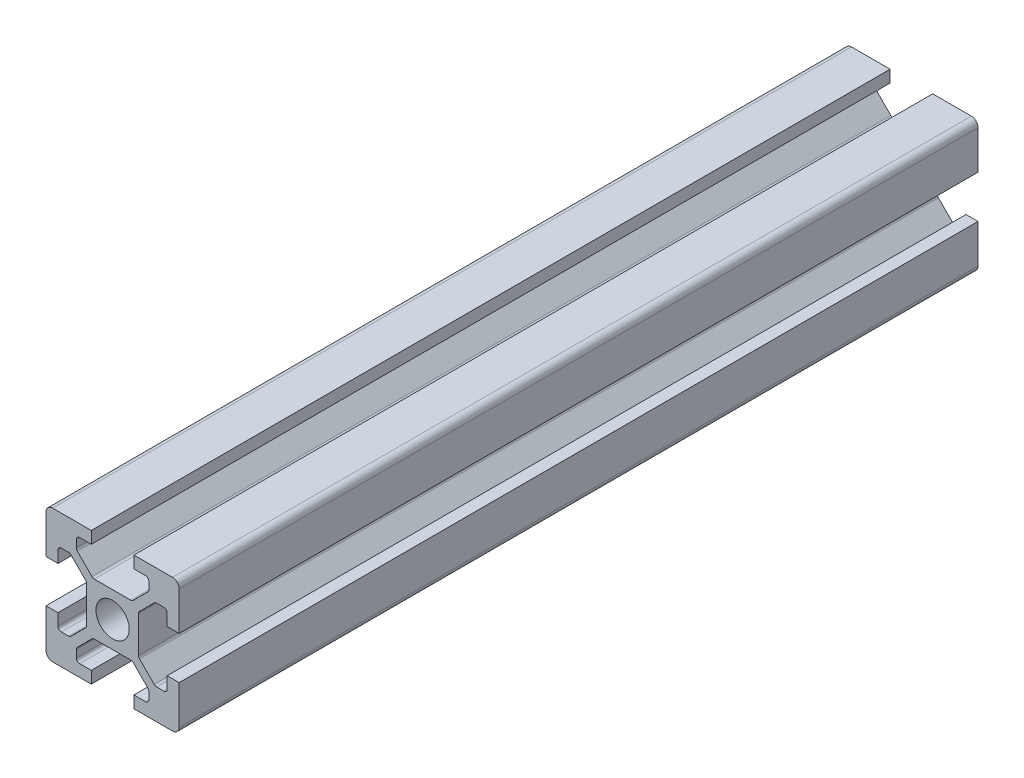
SolidWorks part; units mm, degrees
ref_plane "Front Plane" through (0, 0, 0) normal (0, 0, 1) x (1, 0, 0)
ref_plane "Top Plane" through (0, 0, 0) normal (0, 1, 0) x (1, 0, 0)
ref_plane "Right Plane" through (0, 0, 0) normal (1, 0, 0) x (0, 0, -1)
ref_plane "Plane1" through (0, 0, 0) normal (0, 0, -1) x (-1, 0, 0)
sketch "Sketch1" plane through (0, 0, 0) normal (0, 0, -1) x (-1, 0, 0)
  line L0 (-20, 19) -> (-20, 13.2)
  line L1 (-20, 13.2) -> (-18.2, 13.2)
  line L2 (-18.2, 13.2) -> (-18.2, 14.95)
  line L3 (-17.7, 15.45) -> (-16.6071, 15.45)
  line L4 (-16.2536, 15.3036) -> (-14.0464, 13.0964)
  line L5 (-13.9, 12.7429) -> (-13.9, 7.2571)
  line L6 (-14.0464, 6.9036) -> (-16.2536, 4.6964)
  line L7 (-16.6071, 4.55) -> (-17.7, 4.55)
  line L8 (-18.2, 5.05) -> (-18.2, 6.8)
  line L9 (-18.2, 6.8) -> (-20, 6.8)
  line L10 (-20, 6.8) -> (-20, 1)
  line L11 (-19, 0) -> (-13.2, 0)
  line L12 (-13.2, 0) -> (-13.2, 1.8)
  line L13 (-13.2, 1.8) -> (-14.95, 1.8)
  line L14 (-15.45, 2.3) -> (-15.45, 3.3929)
  line L15 (-15.3036, 3.7464) -> (-13.0964, 5.9536)
  line L16 (-12.7429, 6.1) -> (-7.2571, 6.1)
  line L17 (-6.9036, 5.9536) -> (-4.6964, 3.7464)
  line L18 (-4.55, 3.3929) -> (-4.55, 2.3)
  line L19 (-5.05, 1.8) -> (-6.8, 1.8)
  line L20 (-6.8, 1.8) -> (-6.8, 0)
  line L21 (-6.8, 0) -> (-1, 0)
  line L22 (0, 1) -> (0, 6.8)
  line L23 (0, 6.8) -> (-1.8, 6.8)
  line L24 (-1.8, 6.8) -> (-1.8, 5.05)
  line L25 (-2.3, 4.55) -> (-3.3929, 4.55)
  line L26 (-3.7464, 4.6964) -> (-5.9536, 6.9036)
  line L27 (-6.1, 7.2571) -> (-6.1, 12.7429)
  line L28 (-5.9536, 13.0964) -> (-3.7464, 15.3036)
  line L29 (-3.3929, 15.45) -> (-2.3, 15.45)
  line L30 (-1.8, 14.95) -> (-1.8, 13.2)
  line L31 (-1.8, 13.2) -> (0, 13.2)
  line L32 (0, 13.2) -> (0, 19)
  line L33 (-1, 20) -> (-6.8, 20)
  line L34 (-6.8, 20) -> (-6.8, 18.2)
  line L35 (-6.8, 18.2) -> (-5.05, 18.2)
  line L36 (-4.55, 17.7) -> (-4.55, 16.6071)
  line L37 (-4.6964, 16.2536) -> (-6.9036, 14.0464)
  line L38 (-7.2571, 13.9) -> (-12.7429, 13.9)
  line L39 (-13.0964, 14.0464) -> (-15.3036, 16.2536)
  line L40 (-15.45, 16.6071) -> (-15.45, 17.7)
  line L41 (-14.95, 18.2) -> (-13.2, 18.2)
  line L42 (-13.2, 18.2) -> (-13.2, 20)
  line L43 (-13.2, 20) -> (-19, 20)
  circle A0 centre (-10, 10) radius 2.5
  arc A1 (-19, 20) -> (-20, 19) centre (-19, 19) ccw
  arc A2 (-18.2, 14.95) -> (-17.7, 15.45) centre (-17.7, 14.95) cw
  arc A3 (-16.6071, 15.45) -> (-16.2536, 15.3036) centre (-16.6071, 14.95) cw
  arc A4 (-14.0464, 13.0964) -> (-13.9, 12.7429) centre (-14.4, 12.7429) cw
  arc A5 (-13.9, 7.2571) -> (-14.0464, 6.9036) centre (-14.4, 7.2571) cw
  arc A6 (-16.2536, 4.6964) -> (-16.6071, 4.55) centre (-16.6071, 5.05) cw
  arc A7 (-17.7, 4.55) -> (-18.2, 5.05) centre (-17.7, 5.05) cw
  arc A8 (-20, 1) -> (-19, 0) centre (-19, 1) ccw
  arc A9 (-14.95, 1.8) -> (-15.45, 2.3) centre (-14.95, 2.3) cw
  arc A10 (-15.45, 3.3929) -> (-15.3036, 3.7464) centre (-14.95, 3.3929) cw
  arc A11 (-13.0964, 5.9536) -> (-12.7429, 6.1) centre (-12.7429, 5.6) cw
  arc A12 (-7.2571, 6.1) -> (-6.9036, 5.9536) centre (-7.2571, 5.6) cw
  arc A13 (-4.6964, 3.7464) -> (-4.55, 3.3929) centre (-5.05, 3.3929) cw
  arc A14 (-4.55, 2.3) -> (-5.05, 1.8) centre (-5.05, 2.3) cw
  arc A15 (-1, 0) -> (0, 1) centre (-1, 1) ccw
  arc A16 (-1.8, 5.05) -> (-2.3, 4.55) centre (-2.3, 5.05) cw
  arc A17 (-3.3929, 4.55) -> (-3.7464, 4.6964) centre (-3.3929, 5.05) cw
  arc A18 (-5.9536, 6.9036) -> (-6.1, 7.2571) centre (-5.6, 7.2571) cw
  arc A19 (-6.1, 12.7429) -> (-5.9536, 13.0964) centre (-5.6, 12.7429) cw
  arc A20 (-3.7464, 15.3036) -> (-3.3929, 15.45) centre (-3.3929, 14.95) cw
  arc A21 (-2.3, 15.45) -> (-1.8, 14.95) centre (-2.3, 14.95) cw
  arc A22 (0, 19) -> (-1, 20) centre (-1, 19) ccw
  arc A23 (-5.05, 18.2) -> (-4.55, 17.7) centre (-5.05, 17.7) cw
  arc A24 (-4.55, 16.6071) -> (-4.6964, 16.2536) centre (-5.05, 16.6071) cw
  arc A25 (-6.9036, 14.0464) -> (-7.2571, 13.9) centre (-7.2571, 14.4) cw
  arc A26 (-12.7429, 13.9) -> (-13.0964, 14.0464) centre (-12.7429, 14.4) cw
  arc A27 (-15.3036, 16.2536) -> (-15.45, 16.6071) centre (-14.95, 16.6071) cw
  arc A28 (-15.45, 17.7) -> (-14.95, 18.2) centre (-14.95, 17.7) cw
extrude "Boss-Extrude1" add sketch "Sketch1" against normal blind 300
sketch "Sketch2" plane through (0, 20, 0) normal (0, 1, 0) x (1, 0, 0)
  line L0 (20, -300) -> (20, 0) construction
  line L1 (0, 0) -> (20, 0)
  line L2 (0, 0) -> (0, -180)
  line L3 (0, -180) -> (20, -180)
  line L4 (20, 0) -> (20, -180)
  dimension "D1" = 180
extrude "Cut-Extrude1" cut sketch "Sketch2" against normal blind 30
